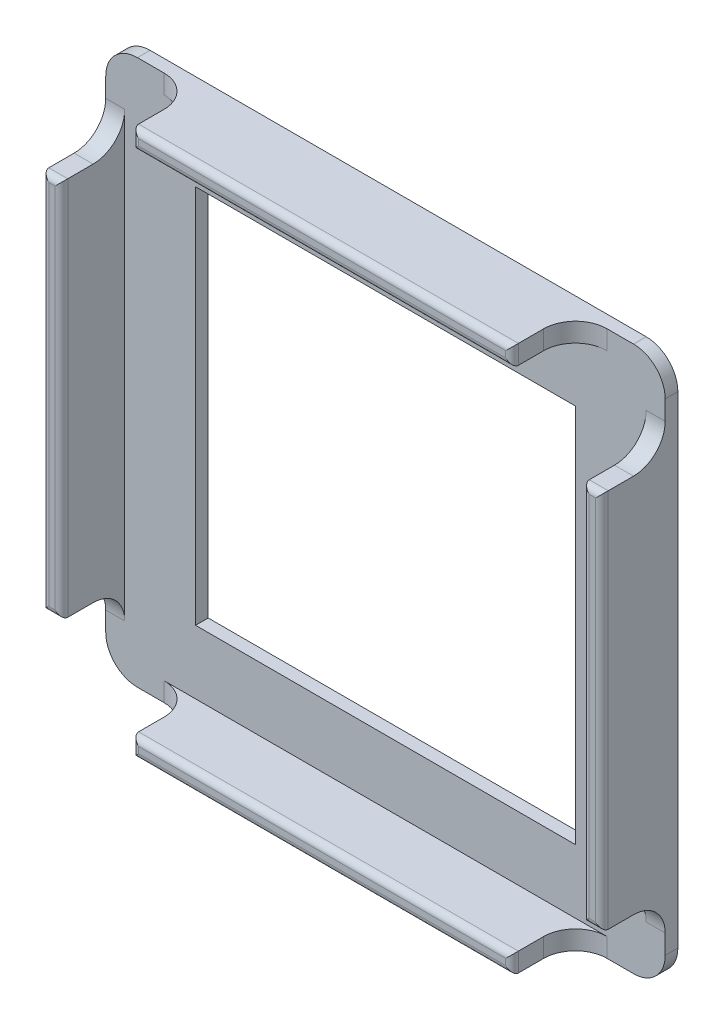
SolidWorks part; units mm, degrees
ref_plane "Front Plane" through (0, 0, 0) normal (0, 0, 1) x (1, 0, 0)
ref_plane "Top Plane" through (0, 0, 0) normal (0, 1, 0) x (1, 0, 0)
ref_plane "Right Plane" through (0, 0, 0) normal (1, 0, 0) x (0, 0, -1)
sketch "Sketch1" plane through (0, 0, 0) normal (0, 0, 1) x (1, 0, 0)
  line L1 (0, 0) -> (88.3722, 0)
  line L2 (0, 0) -> (0, 86.137)
  line L3 (0, 86.137) -> (88.3722, 86.137)
  line L4 (88.3722, 0) -> (88.3722, 86.137)
  dimension "D1" = 88.3722
  dimension "D2" = 86.137
extrude "Boss-Extrude1" add sketch "Sketch1" along normal blind 2
sketch "Sketch2" plane through (0, 0, 2) normal (0, 0, 1) x (1, 0, 0)
  line L0 (0, 86.137) -> (0, 0) construction
  line L1 (0, 73.0685) -> (3, 73.0685)
  line L2 (0, 73.0685) -> (0, 13.0685)
  line L3 (0, 13.0685) -> (3, 13.0685)
  line L4 (3, 73.0685) -> (3, 13.0685)
  line L5 (44.1861, 86.137) -> (44.1861, 0) construction
  line L6 (88.3722, 86.137) -> (0, 86.137) construction
  line L7 (0, 0) -> (88.3722, 0) construction
  line L8 (0, 43.0685) -> (88.3722, 43.0685) construction
  line L9 (88.3722, 0) -> (88.3722, 86.137) construction
  line L10 (88.3722, 73.0685) -> (85.3722, 73.0685)
  line L11 (88.3722, 73.0685) -> (88.3722, 13.0685)
  line L12 (88.3722, 13.0685) -> (85.3722, 13.0685)
  line L13 (85.3722, 73.0685) -> (85.3722, 13.0685)
  line L14 (74.1861, 0) -> (74.1861, 3)
  line L15 (14.1861, 86.137) -> (74.1861, 86.137)
  line L16 (14.1861, 86.137) -> (14.1861, 83.137)
  line L17 (14.1861, 83.137) -> (74.1861, 83.137)
  line L18 (74.1861, 86.137) -> (74.1861, 83.137)
  line L19 (14.1861, 3) -> (74.1861, 3)
  line L20 (14.1861, 0) -> (74.1861, 0)
  line L21 (14.1861, 0) -> (14.1861, 3)
  point P6 (0, 43.0685)
  point P25 (44.1861, 86.137)
  dimension "D1" = 3
  dimension "D2" = 60
  dimension "D3" = 3
  dimension "D4" = 60
extrude "Boss-Extrude2" add sketch "Sketch2" along normal blind 10
fillet "Fillet1" radius 5 4 edges at (88.3722, 86.137, 1) (0, 86.137, 1) (0, 0, 1) (88.3722, 0, 1)
fillet "Fillet2" radius 5 8 edges at (1.5, 13.0685, 2) (14.1861, 1.5, 2) (74.1861, 1.5, 2) (86.8722, 13.0685, 2) (86.8722, 73.0685, 2) (74.1861, 84.637, 2) (14.1861, 84.637, 2) (1.5, 73.0685, 2)
fillet "Fillet3" radius 1 16 edges at (86.8722, 13.0685, 12) (85.3722, 43.0685, 12) (86.8722, 73.0685, 12) (88.3722, 43.0685, 12) (14.1861, 1.5, 12) (44.1861, 3, 12) (74.1861, 1.5, 12) (44.1861, 0, 12) (1.5, 73.0685, 12) (3, 43.0685, 12) (1.5, 13.0685, 12) (0, 43.0685, 12) (44.1861, 86.137, 12) (74.1861, 84.637, 12) (44.1861, 83.137, 12) (14.1861, 84.637, 12)
sketch "Sketch3" plane through (0, 0, 2) normal (0, 0, 1) x (1, 0, 0)
  line L0 (3, 43.0685) -> (85.3722, 43.0685) construction
  line L1 (14.1861, 13.0685) -> (74.1861, 13.0685)
  line L2 (14.1861, 13.0685) -> (14.1861, 73.0685)
  line L3 (14.1861, 73.0685) -> (74.1861, 73.0685)
  line L4 (74.1861, 13.0685) -> (74.1861, 73.0685)
  line L5 (14.1861, 13.0685) -> (74.1861, 73.0685) construction
  line L6 (14.1861, 73.0685) -> (74.1861, 13.0685) construction
  line L7 (3, 8.0685) -> (3, 78.0685) construction
  line L8 (85.3722, 78.0685) -> (85.3722, 8.0685) construction
  line L9 (44.1861, 3) -> (44.1861, 83.137) construction
  line L10 (79.1861, 3) -> (9.1861, 3) construction
  line L11 (9.1861, 83.137) -> (79.1861, 83.137) construction
  point P0 (44.1861, 43.0685)
  point P17 (0, 0)
  point P18 (44.1861, 43.0685)
  dimension "D1" = 60
  dimension "D2" = 60
extrude "Cut-Extrude1" cut sketch "Sketch3" against normal up to next
